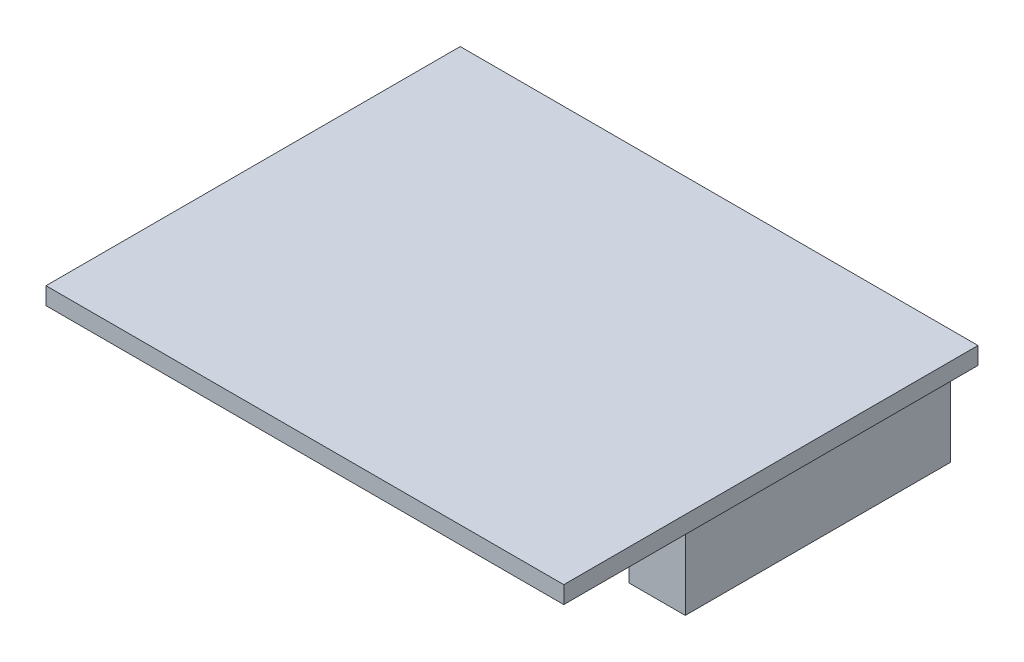
SolidWorks part; units mm, degrees
ref_plane "Front Plane" through (0, 0, 0) normal (0, 0, 1) x (1, 0, 0)
ref_plane "Top Plane" through (0, 0, 0) normal (0, 1, 0) x (1, 0, 0)
ref_plane "Right Plane" through (0, 0, 0) normal (1, 0, 0) x (0, 0, -1)
sketch "Sketch1" plane through (0, 0, 0) normal (0, 1, 0) x (1, 0, 0)
  line L1 (-25.4, -20.32) -> (25.4, -20.32)
  line L2 (-25.4, -20.32) -> (-25.4, 20.32)
  line L3 (-25.4, 20.32) -> (25.4, 20.32)
  line L4 (25.4, -20.32) -> (25.4, 20.32)
  line L5 (-25.4, -20.32) -> (25.4, 20.32) construction
  line L6 (-25.4, 20.32) -> (25.4, -20.32) construction
  point P0 (0, 0)
  dimension "D1" = 40.64
  dimension "D2" = 50.8
extrude "Boss-Extrude1" add sketch "Sketch1" along normal blind 1.7
sketch "Sketch2" plane through (0, 0, 0) normal (0, -1, 0) x (1, 0, 0)
  line L0 (-25.4, -20.32) -> (-25.4, 20.32) construction
  line L1 (-24.4, -19.32) -> (-19.4, -19.32)
  line L2 (-24.4, -19.32) -> (-24.4, 6.68)
  line L3 (-24.4, 6.68) -> (-19.4, 6.68)
  line L4 (-19.4, -19.32) -> (-19.4, 6.68)
  line L5 (-24.4, -19.32) -> (-19.4, 6.68) construction
  line L6 (-24.4, 6.68) -> (-19.4, -19.32) construction
  line L8 (25.4, -20.32) -> (-25.4, -20.32) construction
  point P0 (-21.9, -6.32)
  dimension "D1" = 1
  dimension "D2" = 1
  dimension "D3" = 5
  dimension "D4" = 26
extrude "Boss-Extrude2" add sketch "Sketch2" along normal blind 8.6
ref_plane "Plane1" through (0, 0, 0) normal (-1, 0, 0) x (0, 0, 1)
sketch "Sketch3" plane through (0, 0, 0) normal (0, -1, 0) x (1, 0, 0)
  line L0 (-24.4, -19.32) -> (-19.4, -19.32) construction
  line L1 (18.18, -19.32) -> (23.68, -19.32)
  line L2 (18.18, -19.32) -> (18.18, 6.68)
  line L3 (18.18, 6.68) -> (23.68, 6.68)
  line L4 (23.68, -19.32) -> (23.68, 6.68)
  line L5 (18.18, -19.32) -> (23.68, 6.68) construction
  line L6 (18.18, 6.68) -> (23.68, -19.32) construction
  line L7 (-19.4, 6.68) -> (-24.4, 6.68) construction
  line L8 (-19.4, -19.32) -> (-19.4, 6.68) construction
  point P0 (20.93, -6.32)
  dimension "D1" = 5.5
  dimension "D2" = 37.58
extrude "Boss-Extrude3" add sketch "Sketch3" along normal up to surface (8.6 mm away) up to face at (-21.9, -8.6, -6.32)
